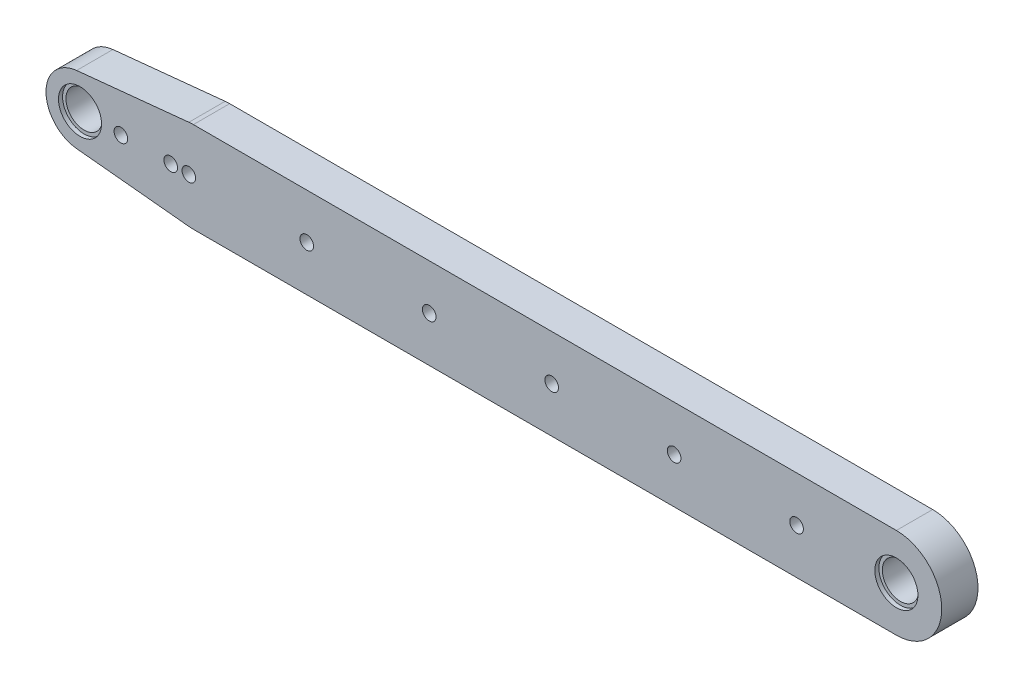
SolidWorks part; units mm, degrees
ref_plane "前视基准面" through (0, 0, 0) normal (0, 0, 1) x (1, 0, 0)
ref_plane "上视基准面" through (0, 0, 0) normal (0, 1, 0) x (1, 0, 0)
ref_plane "右视基准面" through (0, 0, 0) normal (1, 0, 0) x (0, 0, -1)
other "Configuration Table"
sketch "草图1" plane through (0, 0, 0) normal (0, 0, 1) x (1, 0, 0)
  line L0 (-77.5, 0) -> (77.5, 0) construction
  line L1 (-77.5, 10) -> (77.5, 10)
  line L2 (-77.5, -10) -> (77.5, -10)
  line L3 (-77.5, 0) -> (-211.495, 0) construction
  line L4 (-103.25, 7.4624) -> (-78.5, 9.9499)
  line L5 (-103.25, -7.4624) -> (-78.5, -9.9499)
  arc A0 (-77.5, 10) -> (-77.5, -10) centre (-77.5, 0) ccw
  arc A1 (77.5, -10) -> (77.5, 10) centre (77.5, 0) ccw
  circle A2 centre (-77.5, 0) radius 10
  arc A3 (-103.25, 7.4624) -> (-103.25, -7.4624) centre (-102.5, 0) ccw
  circle A4 centre (77.5, 0) radius 4 construction
  circle A5 centre (-102.5, 0) radius 4 construction
  point P3 (0, 0)
  dimension "D1" = 10
  dimension "D4" = 7.5
  dimension "D5" = 8
  dimension "D6" = 8
  dimension "D2" = 180
  dimension "D3" = 25
extrude "凸台-拉伸1" add sketch "草图1" along normal blind 8 contours A2 L2 A1 L1 | A0 A2 | L4 A3 L5 A0
sketch "草图2" plane through (0, 0, 8) normal (0, 0, 1) x (1, 0, 0)
  line L8 (77.5, 10) -> (-77.5, 10)
  line L9 (-78.5, 9.9499) -> (-103.25, 7.4624)
  line L10 (-103.25, -7.4624) -> (-78.5, -9.9499)
  line L11 (-77.5, -10) -> (77.5, -10)
  line L12 (77.5, 10) -> (-77.5, 10)
  line L13 (-78.5, 9.9499) -> (-103.25, 7.4624)
  line L14 (-103.25, -7.4624) -> (-78.5, -9.9499)
  line L15 (-77.5, -10) -> (77.5, -10)
  arc A8 (-77.5, 10) -> (-78.5, 9.9499) centre (-77.5, 0) ccw
  arc A9 (-103.25, 7.4624) -> (-103.25, -7.4624) centre (-102.5, 0) ccw
  arc A10 (-78.5, -9.9499) -> (-77.5, -10) centre (-77.5, 0) ccw
  arc A11 (77.5, -10) -> (77.5, 10) centre (77.5, 0) ccw
  arc A12 (-77.5, 10) -> (-78.5, 9.9499) centre (-77.5, 0) ccw
  arc A13 (-103.25, 7.4624) -> (-103.25, -7.4624) centre (-102.5, 0) ccw
  arc A14 (-78.5, -9.9499) -> (-77.5, -10) centre (-77.5, 0) ccw
  arc A15 (77.5, -10) -> (77.5, 10) centre (77.5, 0) ccw
  dimension "D1" = 0
sketch "草图5" plane through (0, 0, 8) normal (0, 0, 1) x (1, 0, 0)
  line L0 (-137.9457, 0) -> (111.3359, 0) construction
  point P3 (-93.5, 0)
  point P4 (-82.5, 0)
  point P5 (-78.5, 0)
  dimension "D1" = 9
  dimension "D2" = 20
  dimension "D3" = 24
hole_wizard "M3 螺纹孔2" positions "草图5" profile "草图6" tap size "M3" standard "GB" end condition through all
sketch "草图6" plane through (-78.5, 0, 8) normal (1, 0, 0) x (0, -1, 0)
  line L0 (0, 0) -> (0, 8)
  line L1 (0, 8) -> (1.5, 8)
  line L2 (1.5, 8) -> (1.5, 0)
  line L5 (1.5, 0) -> (0, 0)
  line L11 (0, -6.35) -> (0, 107.95) construction
  dimension "通孔螺纹孔钻头直径" = 3
  dimension "通孔螺纹孔钻头深度" = 8
cosmetic thread "孔螺蚊线4" parameters "D2"=3
cosmetic thread "孔螺蚊线5" parameters "D2"=3
cosmetic thread "孔螺蚊线6" parameters "D2"=3
sketch "草图7" plane through (0, 0, 8) normal (0, 0, 1) x (1, 0, 0)
  point P0 (-102.5, 0)
  point P3 (77.5, 0)
hole_wizard "M5 六角头螺栓的柱形沉头孔1" positions "草图7" profile "草图8" counterbore size "M5" standard "GB" end condition through all
sketch "草图8" plane through (-102.5, 0, 8) normal (1, 0, 0) x (0, -1, 0)
  line L0 (0, 0) -> (0, 8)
  line L1 (0, 8) -> (4, 8)
  line L3 (4, 8) -> (4, 0.9)
  line L4 (4, 0.9) -> (4.75, 0.9)
  line L5 (4.75, 0.9) -> (4.75, 0)
  line L7 (4.75, 0) -> (0, 0)
  line L11 (0, -6.35) -> (0, 107.95) construction
  dimension "通孔孔直径" = 8
  dimension "通孔孔深度" = 8
  dimension "柱形沉头孔直径" = 9.5
  dimension "柱形沉头孔深度" = 0.9
sketch "草图11" plane through (0, 0, 8) normal (0, 0, 1) x (1, 0, 0)
  line L0 (-102.5, 0) -> (77.5, 0) construction
  circle A0 centre (-52.5, 0) radius 1.5
  circle A1 centre (-25.5, 0) radius 1.5
  circle A2 centre (1.5, 0) radius 1.5
  circle A3 centre (28.5, 0) radius 1.5
  circle A4 centre (55.5, 0) radius 1.5
  dimension "D2" = 3
  dimension "D1" = 50
  dimension "D4" = 27
  dimension "D3" = 5
extrude "切除-拉伸1" cut sketch "草图11" against normal through all both and the other way through all
equation "\"BigArm\"= 180mm"
